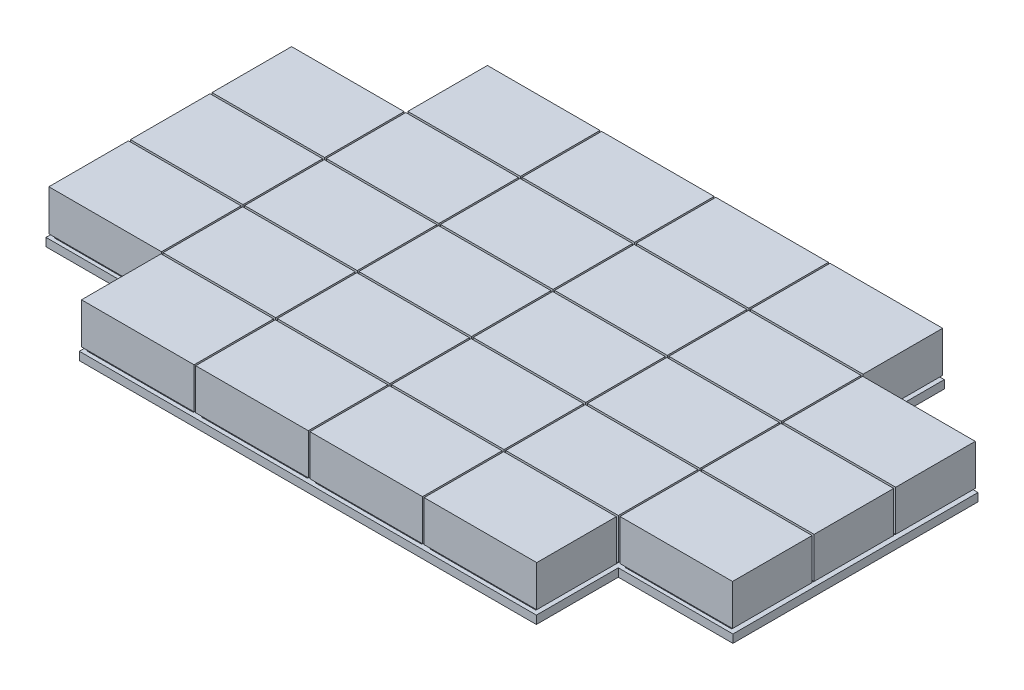
SolidWorks part; units mm, degrees
ref_plane "Front Plane" through (0, 0, 0) normal (0, 0, 1) x (1, 0, 0)
ref_plane "Top Plane" through (0, 0, 0) normal (0, 1, 0) x (1, 0, 0)
ref_plane "Right Plane" through (0, 0, 0) normal (1, 0, 0) x (0, 0, -1)
sketch "Sketch1" plane through (0, 0, 0) normal (0, 1, 0) x (1, 0, 0)
  line L1 (-35.5, -125) -> (35.5, -125)
  line L2 (-35.5, -125) -> (-35.5, 125)
  line L3 (-35.5, 125) -> (35.5, 125)
  line L4 (35.5, -125) -> (35.5, 125)
  line L5 (-35.5, -125) -> (35.5, 125) construction
  line L6 (-35.5, 125) -> (35.5, -125) construction
  point P0 (0, 0)
  dimension "D1" = 71
  dimension "D2" = 250
extrude "Boss-Extrude1" add sketch "Sketch1" along normal blind 5
sketch "Sketch2" plane through (0, 5, 0) normal (0, 1, 0) x (1, 0, 0)
  line L0 (0, 0) -> (0, -125) construction
  line L1 (-35.5, -125) -> (35.5, -125) construction
  line L3 (-32.5, -77.5) -> (32.5, -77.5)
  line L4 (-32.5, -77.5) -> (-32.5, -122.5)
  line L5 (-32.5, -122.5) -> (32.5, -122.5)
  line L6 (32.5, -77.5) -> (32.5, -122.5)
  line L7 (-32.5, -77.5) -> (32.5, -122.5) construction
  line L8 (-32.5, -122.5) -> (32.5, -77.5) construction
  point P5 (0, -100)
  dimension "D1" = 65
  dimension "D2" = 45
  dimension "D3" = 2.5
extrude "Boss-Extrude3" add sketch "Sketch2" along normal blind 2
pattern_linear "LPattern1" count 5 spacing 50 along (0, 0, -1) of "Boss-Extrude3"
sketch "Sketch3" plane through (0, 7, 0) normal (0, 1, 0) x (1, 0, 0)
  line L0 (0, 0) -> (0, -122.5) construction
  line L1 (-32.5, -122.5) -> (32.5, -122.5) construction
  line L2 (-35.5, 125) -> (-35.5, -125) construction
  line L3 (-34.5, -75.2576) -> (34.5, -75.2576)
  line L4 (-34.5, -75.2576) -> (-34.5, -124.0124)
  line L5 (-34.5, -124.0124) -> (34.5, -124.0124)
  line L6 (34.5, -75.2576) -> (34.5, -124.0124)
  line L7 (-34.5, -75.2576) -> (34.5, -124.0124) construction
  line L8 (-34.5, -124.0124) -> (34.5, -75.2576) construction
  point P5 (0, -99.635)
  dimension "D1" = 1
extrude "Boss-Extrude8" add sketch "Sketch3" along normal blind 25
pattern_linear "LPattern5" count 5 spacing 50 along (0, 0, -1) of "Boss-Extrude8"
sketch "Sketch5" plane through (0, 0, 0) normal (0, 1, 0) x (1, 0, 0)
  line L0 (0, 0) -> (208.2024, 0) construction
pattern_linear "LPattern6" count 6 spacing 70 along (1, 0, 0) of "Boss-Extrude1", "Boss-Extrude3", "LPattern1", "Boss-Extrude8", "LPattern5"
sketch "Sketch6" plane through (0, 5, 0) normal (0, 1, 0) x (1, 0, 0)
  line L1 (315.2588, 75.4257) -> (386.1769, 75.4257)
  line L2 (315.2588, 75.4257) -> (315.2588, 125.8727)
  line L3 (315.2588, 125.8727) -> (386.1769, 125.8727)
  line L4 (386.1769, 75.4257) -> (386.1769, 125.8727)
  line L5 (315.2588, -74.7745) -> (387.4228, -74.7745)
  line L6 (315.2588, -74.7745) -> (315.2588, -125.7378)
  line L7 (315.2588, -125.7378) -> (387.4228, -125.7378)
  line L8 (387.4228, -74.7745) -> (387.4228, -125.7378)
  line L9 (35.1617, 75.4257) -> (-38.1734, 75.4257)
  line L10 (35.1617, 75.4257) -> (35.1617, 127.6484)
  line L11 (35.1617, 127.6484) -> (-38.1734, 127.6484)
  line L12 (-38.1734, 75.4257) -> (-38.1734, 127.6484)
  line L13 (35.1617, -74.7745) -> (-38.1734, -74.7745)
  line L14 (35.1617, -74.7745) -> (35.1617, -130.5235)
  line L15 (35.1617, -130.5235) -> (-38.1734, -130.5235)
  line L16 (-38.1734, -74.7745) -> (-38.1734, -130.5235)
extrude "Cut-Extrude1" cut sketch "Sketch6" against normal through all both and the other way through all
